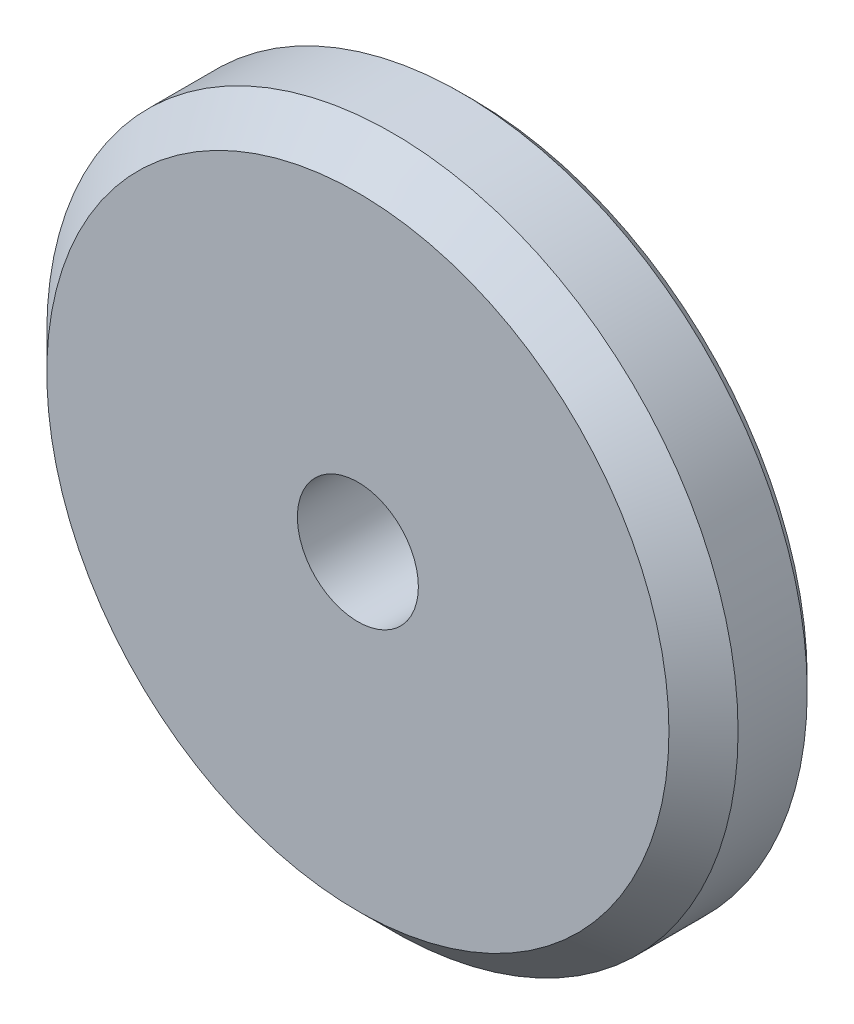
SolidWorks part; units mm, degrees
material "AISI 1020"
ref_plane "Спереди" through (0, 0, 0) normal (0, 0, 1) x (1, 0, 0)
ref_plane "Сверху" through (0, 0, 0) normal (0, 1, 0) x (1, 0, 0)
ref_plane "Справа" through (0, 0, 0) normal (1, 0, 0) x (0, 0, -1)
sketch "Эскиз2" plane through (0, 0, 0) normal (0, 0, 1) x (1, 0, 0)
  line L0 (-46.6361, -16.5855) -> (210.7658, -138.9344) construction
  circle A0 centre (0, 0) radius 5.25
  circle A1 centre (0, 0) radius 30
  dimension "D1" = 10.5
  dimension "D2" = 5
extrude "Бобышка-Вытянуть1" add sketch "Эскиз2" along normal blind 10
chamfer "Фаска1" distance 3 angle 45 1 edges at (30, 0, 10)
chamfer "Фаска2" distance 1 angle 45 1 edges at (30, 0, 0)
